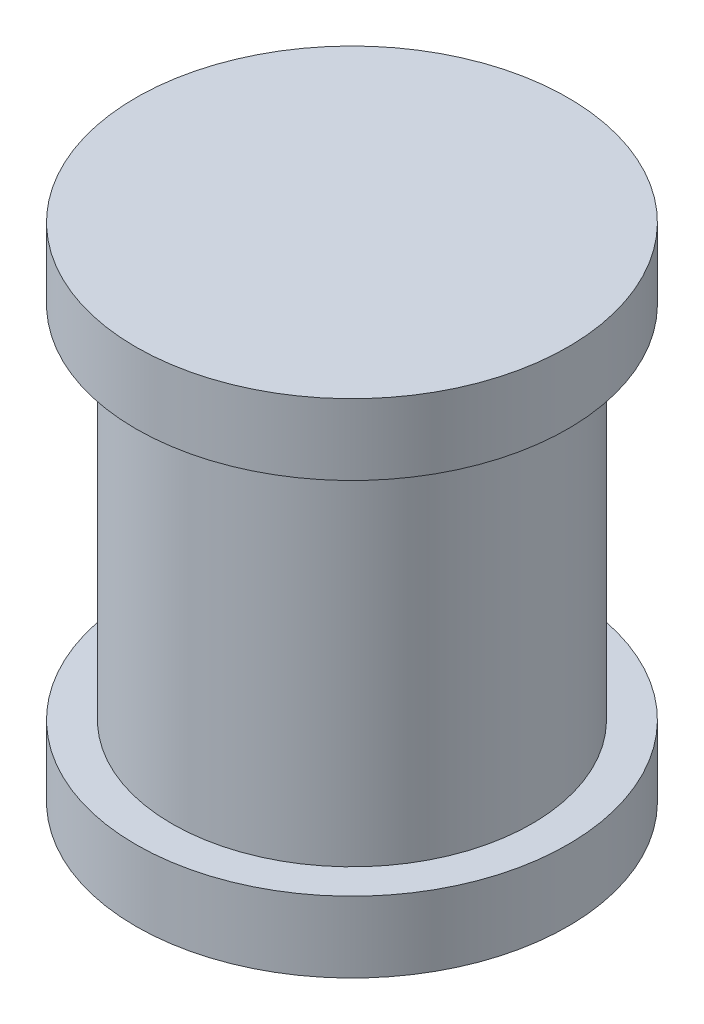
SolidWorks part; units mm, degrees
ref_plane "Front Plane" through (0, 0, 0) normal (0, 0, 1) x (1, 0, 0)
ref_plane "Top Plane" through (0, 0, 0) normal (0, 1, 0) x (1, 0, 0)
ref_plane "Right Plane" through (0, 0, 0) normal (1, 0, 0) x (0, 0, -1)
sketch "Sketch1" plane through (0, 0, 0) normal (0, 1, 0) x (1, 0, 0)
  circle A0 centre (0, 0) radius 12.7
  dimension "D1" = 25.4
extrude "Boss-Extrude1" add sketch "Sketch1" along normal mid plane 25.4
sketch "Sketch2" plane through (0, 12.7, 0) normal (0, 1, 0) x (1, 0, 0)
  circle A0 centre (0, 0) radius 15.24
  dimension "D1" = 30.48
extrude "Boss-Extrude2" add sketch "Sketch2" along normal blind 5 contours A0
ref_plane "Plane1" through (0, 0, 0) normal (0, 1, 0) x (1, 0, 0)
mirror "Mirror1" about plane through (0, 0, 0) normal (0, 1, 0) of "Boss-Extrude2"
